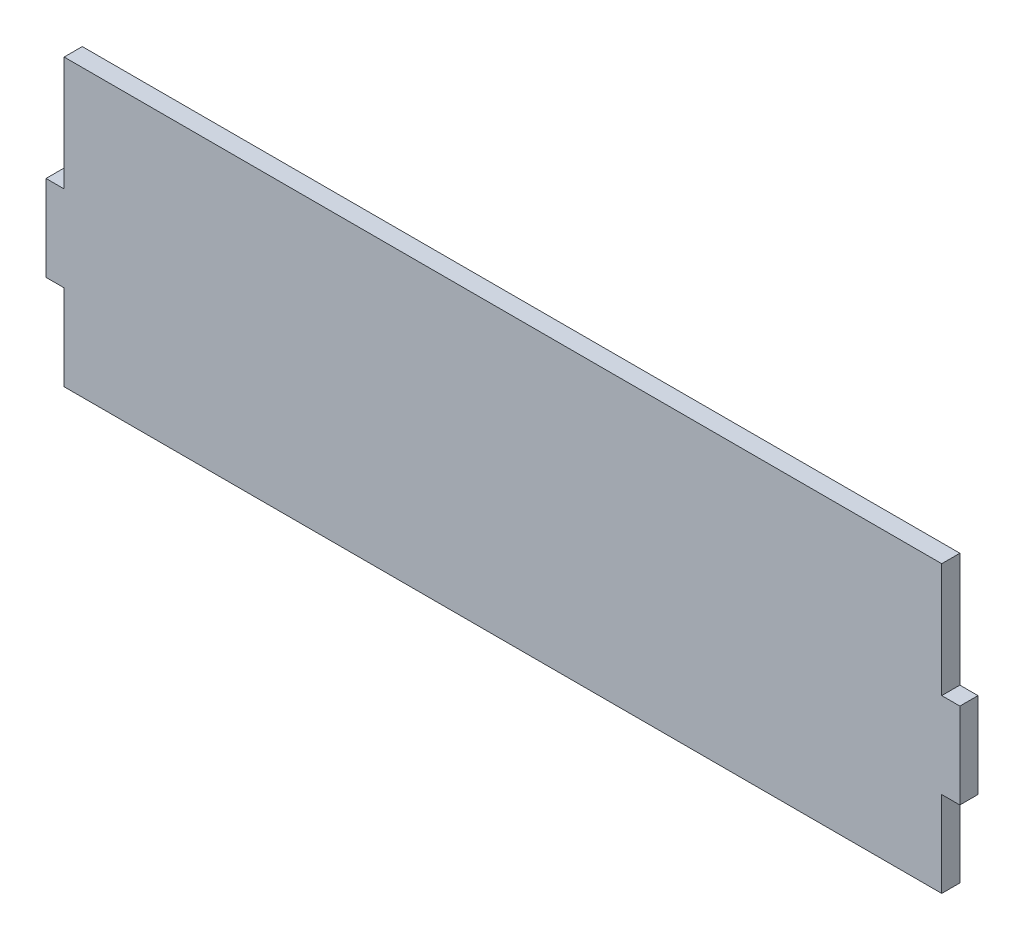
SolidWorks part; units mm, degrees
ref_plane "Front Plane" through (0, 0, 0) normal (0, 0, 1) x (1, 0, 0)
ref_plane "Top Plane" through (0, 0, 0) normal (0, 1, 0) x (1, 0, 0)
ref_plane "Right Plane" through (0, 0, 0) normal (1, 0, 0) x (0, 0, -1)
sketch "Sketch1" plane through (0, 0, 0) normal (0, 0, 1) x (1, 0, 0)
  line L0 (-1325.3446, 0) -> (1774.5449, 0) construction
  line L1 (0, 443.621) -> (0, -444.8653) construction
  line L2 (-76.825, 0) -> (76.825, 0)
  line L3 (76.825, 0) -> (76.825, 15)
  line L4 (76.825, 15) -> (80, 15)
  line L5 (80, 15) -> (80, 30)
  line L6 (80, 30) -> (76.825, 30)
  line L7 (76.825, 30) -> (76.825, 50)
  line L8 (76.825, 50) -> (-76.825, 50)
  line L9 (-76.825, 30) -> (-76.825, 50)
  line L10 (-80, 30) -> (-76.825, 30)
  line L11 (-80, 15) -> (-80, 30)
  line L12 (-76.825, 15) -> (-80, 15)
  line L13 (-76.825, 0) -> (-76.825, 15)
  point P14 (0, 0)
  point P15 (0, 50)
  dimension "D1" = 76.825
  dimension "D2" = 3.175
  dimension "D3" = 15
  dimension "D4" = 15
  dimension "D5" = 3.175
  dimension "D6" = 20
extrude "Boss-Extrude1" add sketch "Sketch1" along normal blind 3.175
